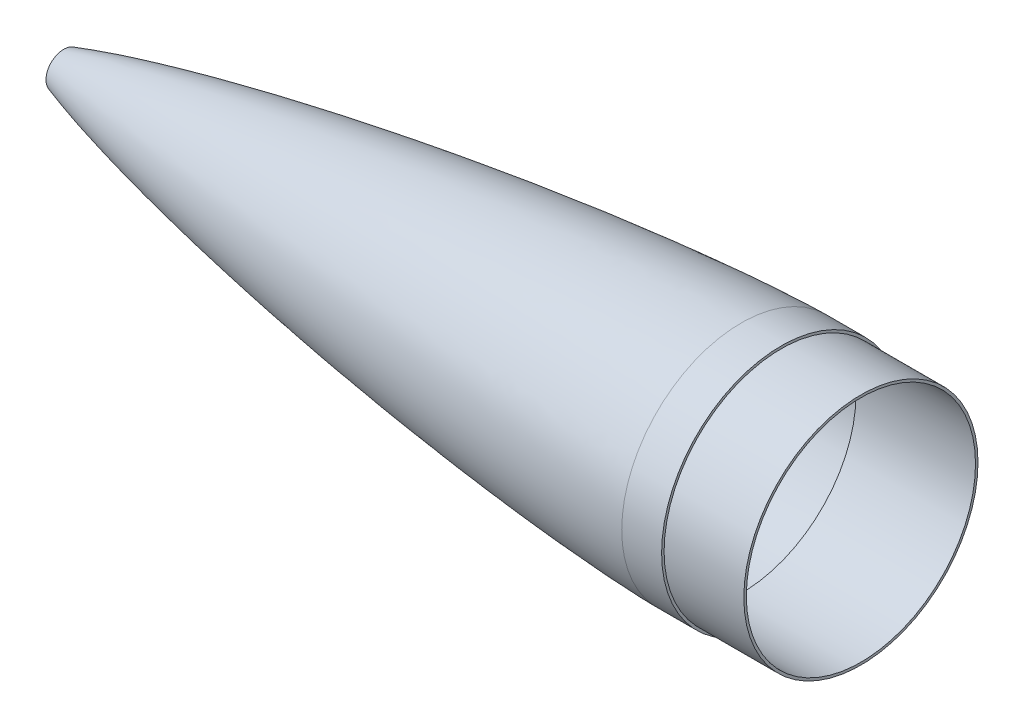
SolidWorks part; units mm, degrees
material "Hexcel AS4C (3000 Filaments)"
ref_plane "Front Plane" through (0, 0, 0) normal (0, 0, 1) x (1, 0, 0)
ref_plane "Top Plane" through (0, 0, 0) normal (0, 1, 0) x (1, 0, 0)
ref_plane "Right Plane" through (0, 0, 0) normal (1, 0, 0) x (0, 0, -1)
sketch "Sketch6" plane through (0, 0, 0) normal (0, 0, 1) x (1, 0, 0)
  line L0 (-61.6447, 0) -> (914.4764, 0) construction
  line L1 (50.8, 22.5304) -> (50.8, 6.35)
  line L2 (50.8, 6.35) -> (53.975, 6.35)
  line L3 (53.975, 6.35) -> (53.975, 20.2276)
  line L4 (914.4, 152.4) -> (965.2, 152.4)
  line L5 (965.2, 152.4) -> (965.2, 149.225)
  line L6 (965.2, 149.225) -> (1066.8, 149.225)
  line L7 (1066.8, 149.225) -> (1066.8, 146.05)
  line L8 (1066.8, 146.05) -> (914.4108, 146.05)
  line L9 (914.4108, 146.05) -> (914.4108, 149.225)
  spline S0 degree 4 poles (0.7109, 0.9249) (0.8194, 1.0297) (1.0401, 1.2349) (1.4358, 1.5745) (2.113, 2.1031) (3.1076, 2.8103) (4.6829, 3.824) (7.1818, 5.2703) (10.3353, 6.9058) (13.9855, 8.6421) (18.4315, 10.6148) (23.2827, 12.6355) (27.8273, 14.4199) (32.0456, 16.0063) (35.3451, 17.212) (37.7085, 18.0607) (40.0869, 18.9004) (42.4489, 19.7217) (44.8547, 20.5452) (47.1736, 21.3287) (50.0431, 22.2836) (52.5896, 23.1187) (57.1138, 24.5817) (62.1376, 26.1632) (68.4729, 28.1134) (76.3898, 30.4748) (85.386, 33.0811) (95.2414, 35.8415) (106.1049, 38.7887) (117.8122, 41.8678) (130.4239, 45.085) (143.9074, 48.4172) (158.286, 51.8608) (172.6821, 55.208) (187.101, 58.4688) (201.5363, 61.648) (215.9891, 64.7518) (234.0733, 68.5424) (255.8026, 72.9566) (281.1895, 77.9247) (306.6148, 82.6926) (328.4324, 86.6462) (350.2681, 90.4977) (372.1212, 94.25) (397.6401, 98.4881) (426.8345, 103.1476) (456.0568, 107.6286) (485.3054, 111.935) (514.5788, 116.0692) (543.8758, 120.0326) (573.1954, 123.8249) (602.5369, 127.4447) (631.8994, 130.8892) (661.2825, 134.1539) (698.0365, 138.0018) (742.1809, 142.23) (786.3738, 145.927) (830.6152, 148.9895) (864.1455, 150.8175) (884.9324, 151.7025) (900.3474, 152.1772) (908.3769, 152.3409) (912.3922, 152.3932) (914.4, 152.4) knots 0 0 0 0 0 0.000648 0.001296 0.002242 0.003694 0.005895 0.00935 0.014656 0.018967 0.023278 0.030267 0.037257 0.039961 0.042665 0.045369 0.048073 0.050777 0.053481 0.056184 0.058888 0.062862 0.066835 0.074782 0.082729 0.090676 0.102753 0.114829 0.126906 0.138983 0.154877 0.170771 0.186664 0.202558 0.218452 0.234346 0.250239 0.266133 0.297921 0.329708 0.361496 0.37739 0.393283 0.425071 0.456858 0.488646 0.520434 0.552221 0.584009 0.615796 0.647584 0.679371 0.711159 0.742946 0.774734 0.838309 0.901884 0.933672 0.965459 0.98273 0.991365 1 1 1 1 1 construction
  spline S1 degree 4 poles (50.8, 22.5304) (51.626, 22.8019) (53.2474, 23.3314) (57.1138, 24.5817) (62.1376, 26.1632) (68.4729, 28.1134) (76.3898, 30.4748) (85.386, 33.0811) (95.2414, 35.8415) (106.1049, 38.7887) (117.8122, 41.8678) (130.4239, 45.085) (143.9074, 48.4172) (158.286, 51.8608) (172.6821, 55.208) (187.101, 58.4688) (201.5363, 61.648) (215.9891, 64.7518) (234.0733, 68.5424) (255.8026, 72.9566) (281.1895, 77.9247) (306.6148, 82.6926) (328.4324, 86.6462) (350.2681, 90.4977) (372.1212, 94.25) (397.6401, 98.4881) (426.8345, 103.1476) (456.0568, 107.6286) (485.3054, 111.935) (514.5788, 116.0692) (543.8758, 120.0326) (573.1954, 123.8249) (602.5369, 127.4447) (631.8994, 130.8892) (661.2825, 134.1539) (698.0365, 138.0018) (742.1809, 142.23) (786.3738, 145.927) (830.6152, 148.9895) (864.1455, 150.8175) (884.9324, 151.7025) (900.3474, 152.1772) (908.3769, 152.3409) (912.3922, 152.3932) (914.4, 152.4) knots 0.058888 0.058888 0.058888 0.058888 0.058888 0.062862 0.066835 0.074782 0.082729 0.090676 0.102753 0.114829 0.126906 0.138983 0.154877 0.170771 0.186664 0.202558 0.218452 0.234346 0.250239 0.266133 0.297921 0.329708 0.361496 0.37739 0.393283 0.425071 0.456858 0.488646 0.520434 0.552221 0.584009 0.615796 0.647584 0.679371 0.711159 0.742946 0.774734 0.838309 0.901884 0.933672 0.965459 0.98273 0.991365 1 1 1 1 1
  spline S2 degree 1 poles (51.7917, 19.5142) (914.4108, 149.225) knots 0 0 1 1 construction
  spline S3 degree 3 poles (51.7917, 19.5142) (52.3018, 19.6819) (53.3014, 20.0091) (54.9287, 20.5374) (56.6361, 21.0877) (58.8672, 21.801) (61.5224, 22.6387) (64.7365, 23.6378) (68.0235, 24.6466) (72.3944, 25.9697) (77.8023, 27.5732) (84.3723, 29.4771) (93.1182, 31.9541) (108.4668, 36.1652) (130.4916, 41.8757) (165.8703, 50.4899) (210.3031, 60.4494) (281.6931, 75.068) (371.3475, 91.3103) (479.375, 108.2298) (569.6849, 120.3768) (642.0768, 128.9125) (696.4384, 134.6926) (750.8635, 139.8007) (796.2675, 143.4252) (832.6178, 145.8603) (859.8907, 147.4162) (882.6287, 148.4363) (898.5341, 148.9465) (907.6277, 149.151) (912.1473, 149.2173) (914.4108, 149.225) knots 0.058888 0.058888 0.058888 0.058888 0.060726 0.062565 0.064403 0.066241 0.069917 0.073593 0.077269 0.080946 0.088298 0.095651 0.103003 0.117708 0.147118 0.176527 0.235347 0.294166 0.411805 0.529444 0.647083 0.705903 0.764722 0.823542 0.882361 0.911771 0.941181 0.97059 0.985295 0.992648 1 1 1 1 only from (53.975, 20.2276) to (914.4108, 149.225)
  dimension "D2" = 3.175
  dimension "D3" = 6.35
  dimension "D4" = 3.175
  dimension "D5" = 101.6
  dimension "D6" = 50.8
  dimension "D7" = 3.175
  dimension "D1" = 3.175
revolve "Revolve1" add sketch "Sketch6" angle 360 about L0
